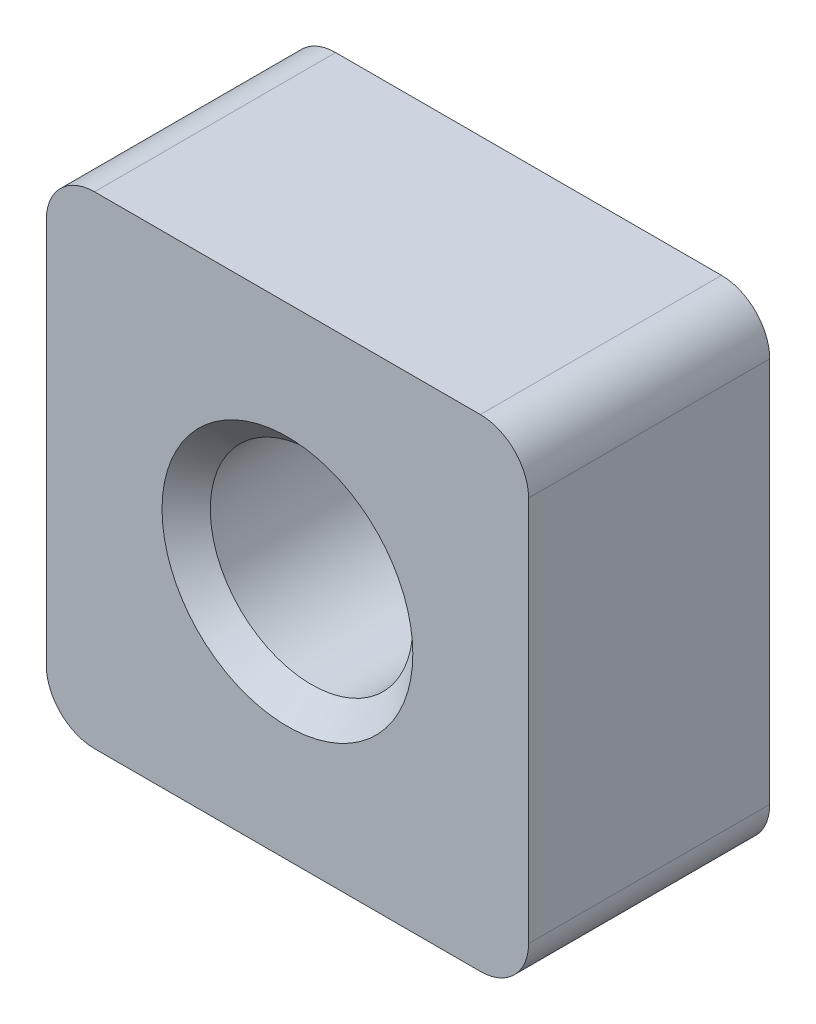
SolidWorks part; units mm, degrees
ref_plane "Спереди" through (0, 0, 0) normal (0, 0, 1) x (1, 0, 0)
ref_plane "Сверху" through (0, 0, 0) normal (0, 1, 0) x (1, 0, 0)
ref_plane "Справа" through (0, 0, 0) normal (1, 0, 0) x (0, 0, -1)
sketch "Эскиз1" plane through (0, 0, 0) normal (0, 0, 1) x (1, 0, 0)
  line L1 (-5, -5) -> (5, -5)
  line L2 (-5, -5) -> (-5, 5)
  line L3 (-5, 5) -> (5, 5)
  line L4 (5, -5) -> (5, 5)
  line L5 (-5, -5) -> (5, 5) construction
  line L6 (-5, 5) -> (5, -5) construction
  point P0 (0, 0)
  dimension "D1" = 10
extrude "Бобышка-Вытянуть1" add sketch "Эскиз1" along normal blind 5
hole_wizard "Отверстие обработанное метчиком M51" positions "Эскиз2" profile "Эскиз3" tap size "M5" standard "ISO" end condition through all
sketch "Эскиз2" plane through (0, 0, 5) normal (0, 0, 1) x (1, 0, 0)
  point P0 (0, 0)
sketch "Эскиз3" plane through (0, 0, 5) normal (1, 0, 0) x (0, -1, 0)
  line L0 (0, 0) -> (0, 5)
  line L1 (0, 5) -> (2.6, 5)
  line L2 (2.1, 4.5) -> (2.1, 0.5)
  line L3 (2.1, 0.5) -> (2.6, 0)
  line L5 (2.6, 0) -> (0, 0)
  line L6 (-2.1, 0.5) -> (-2.6, 0) construction
  line L7 (2.6, 5) -> (2.1, 4.5)
  line L8 (-2.6, 5) -> (-2.1, 4.5) construction
  line L11 (0, -6.35) -> (0, 107.95) construction
  dimension "Диаметр проходного сверла" = 4.2
  dimension "Глубина проходного сверла" = 5
  dimension "Диаметр передней зенковки" = 5.2
  dimension "Угол передней зенковки" = 90
  dimension "Диаметр задней зенковки" = 5.2
  dimension "Угол задней зенковки" = 90
cosmetic thread "Отверстие резьбы1" parameters "D2"=5
fillet "Скругление1" radius 1 4 edges at (5, 5, 2.5) (-5, 5, 2.5) (5, -5, 2.5) (-5, -5, 2.5)
